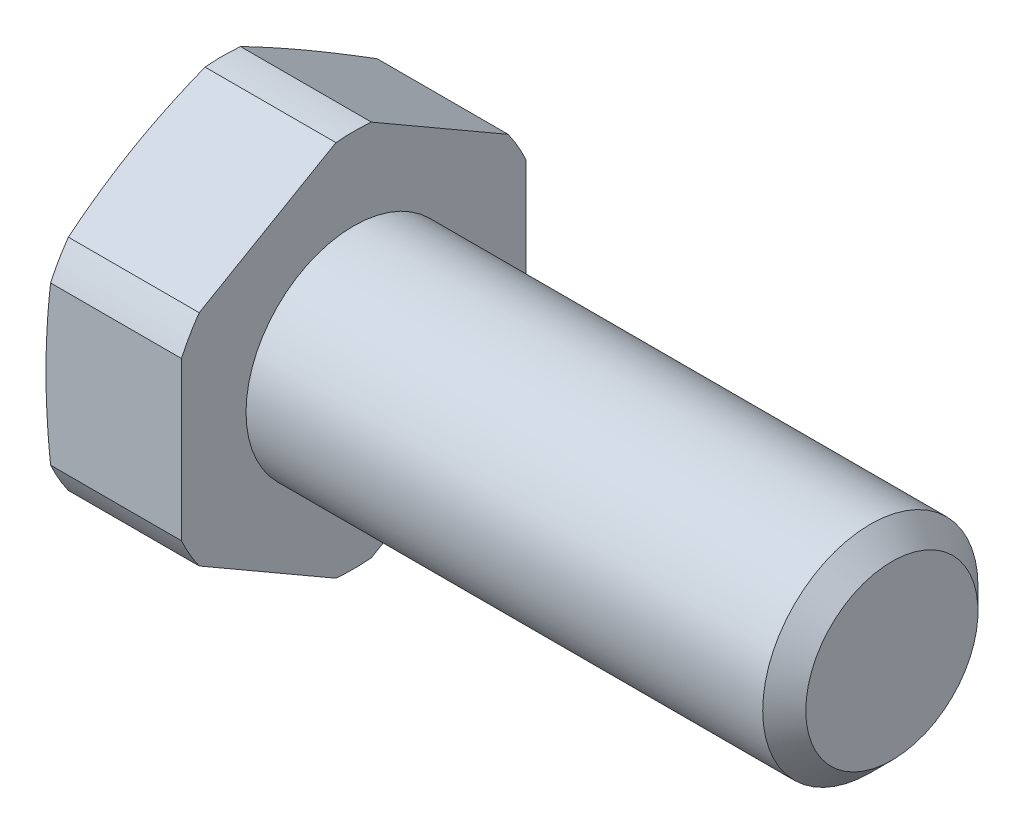
SolidWorks part; units mm, degrees
ref_plane "Спереди" through (0, 0, 0) normal (0, 0, 1) x (1, 0, 0)
ref_plane "Сверху" through (0, 0, 0) normal (0, 1, 0) x (1, 0, 0)
ref_plane "Справа" through (0, 0, 0) normal (1, 0, 0) x (0, 0, -1)
sketch "Эскиз1" plane through (0, 0, 0) normal (0, 0, 1) x (1, 0, 0)
  line L0 (-1000, 0) -> (49000, 0) construction
  line L1 (-6.4, 0) -> (-6.4, 7.6)
  line L2 (-6.4, 7.6) -> (-6.0785, 8.8)
  line L3 (-6.0785, 8.8) -> (0, 8.8)
  line L4 (0, 8.8) -> (0, 5)
  line L5 (0, 5) -> (24, 5)
  line L6 (25, 4) -> (25, 0)
  line L7 (25, 5) -> (25.75, 6.299) construction
  line L8 (25.75, 6.299) -> (26.5, 5) construction
  line L9 (26.5, 5) -> (25, 5) construction
  line L10 (25.75, 6.299) -> (25.75, 5) construction
  line L11 (25.75, 6.299) -> (0.75, 6.299) construction
  line L12 (24, 5) -> (25, 4)
  line L13 (25, 5) -> (24.5, 4.5) construction
  line L14 (-6.4, 7.6) -> (-22.4, 7.6) construction
  line L15 (-6.4, 0) -> (25, 0)
  dimension "l_" = 25
  dimension "b_" = 25
  dimension "_d_" = 10
  dimension "D" = 15.2
  dimension "k_" = 6.4
  dimension "e_" = 17.6
  dimension "shag_" = 1.5
  dimension "dr" = 1.299
  dimension "D1" = 1
  dimension "D2" = 15
  dimension "S_" = 16
revolve "Повернуть1" add sketch "Эскиз1" angle 360 about L0
cosmetic thread "Условное изображение резьбы1" parameters "D1"=25, "D2"=7.4019
sketch "Эскиз2" plane through (-6.4, 0, 0) normal (-1, 0, 0) x (0, 0, 1)
  line L1 (0, 9.2376) -> (-8, 4.6188)
  line L2 (-8, 4.6188) -> (-8, -4.6188)
  line L3 (-8, -4.6188) -> (0, -9.2376)
  line L4 (0, -9.2376) -> (8, -4.6188)
  line L5 (8, -4.6188) -> (8, 4.6188)
  line L6 (8, 4.6188) -> (0, 9.2376)
  circle A0 centre (0, 0) radius 8 construction
  dimension "D1" = 16
extrude "Вырез-Вытянуть1" cut sketch "Эскиз2" against normal up to surface (31.4 mm away) flip side to cut up to face at (25, 0, 4)
other "PropertyManager"
equation "\"D1@Эскиз1\"=\"_d_@Эскиз1\"/10"
equation "\"D@Эскиз1\"=\"S_@Эскиз1\"*0.95"
equation "\"D1@Эскиз2\"=\"S_@Эскиз1\""
equation "\"D1@Условное изображение резьбы1\"=\"b_@Эскиз1\""
equation "\"D2@Условное изображение резьбы1\"=\"_d_@Эскиз1\"-\"dr@Эскиз1\"*2"
